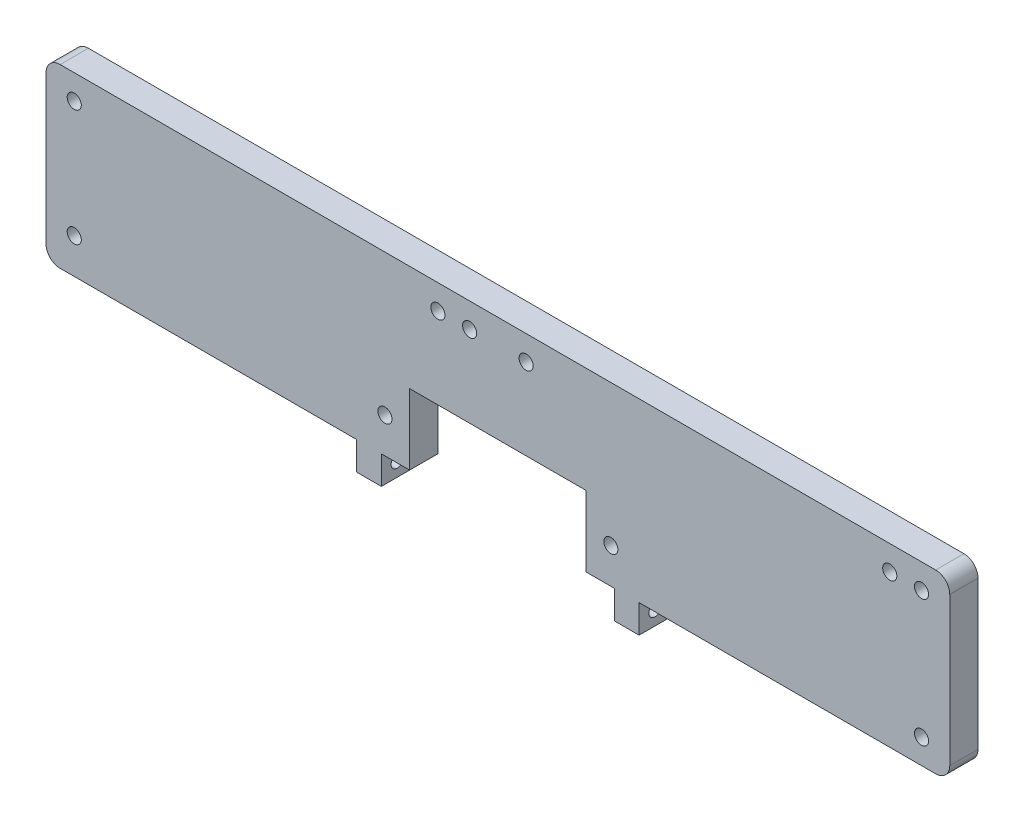
SolidWorks part; units mm, degrees
material "ABS"
ref_plane "Front Plane" through (0, 0, 0) normal (0, 0, 1) x (1, 0, 0)
ref_plane "Top Plane" through (0, 0, 0) normal (0, 1, 0) x (1, 0, 0)
ref_plane "Right Plane" through (0, 0, 0) normal (1, 0, 0) x (0, 0, -1)
sketch "Sketch1" plane through (0, 0, 0) normal (0, 0, 1) x (1, 0, 0)
  line L1 (-127.7162, 72.1061) -> (128.2838, 72.1061)
  line L2 (-127.7162, 72.1061) -> (-127.7162, 22.1061)
  line L3 (-127.7162, 22.1061) -> (128.2838, 22.1061)
  line L4 (128.2838, 72.1061) -> (128.2838, 22.1061)
  circle A1 centre (120.2838, 65.1061) radius 2
  circle A2 centre (111.2838, 65.1061) radius 2
  circle A3 centre (8.2838, 65.1061) radius 2
  circle A4 centre (-7.7162, 65.1061) radius 2
  circle A5 centre (-16.7162, 65.1061) radius 2
  circle A6 centre (-119.7162, 65.1061) radius 2
  dimension "D3" = 4
  dimension "D1" = 256
  dimension "D2" = 50
  dimension "D4" = 7
  dimension "D5" = 9
  dimension "D6" = 8
  dimension "D7" = 103
  dimension "D8" = 16
  dimension "D9" = 9
  dimension "D10" = 103
extrude "Boss-Extrude1" add sketch "Sketch1" along normal blind 8
fillet "Fillet1" radius 4 4 edges at (-127.7162, 22.1061, 4) (128.2838, 22.1061, 4) (128.2838, 72.1061, 4) (-127.7162, 72.1061, 4)
sketch "Sketch2" plane through (0, 0, 8) normal (0, 0, 1) x (1, 0, 0)
  line L0 (-123.7162, 22.1061) -> (124.2838, 22.1061) construction
  line L1 (-24.7162, 34.1061) -> (25.2838, 34.1061)
  line L2 (-24.7162, 34.1061) -> (-24.7162, 22.1061)
  line L3 (-24.7162, 22.1061) -> (25.2838, 22.1061)
  line L4 (25.2838, 34.1061) -> (25.2838, 22.1061)
  line L5 (-127.7162, 68.1061) -> (-127.7162, 26.1061) construction
  line L7 (-32.7162, 22.1061) -> (-39.7162, 22.1061)
  line L8 (-32.7162, 22.1061) -> (-32.7162, 14.1061)
  line L9 (-32.7162, 14.1061) -> (-39.7162, 14.1061)
  line L10 (-39.7162, 22.1061) -> (-39.7162, 14.1061)
  line L11 (33.2838, 22.1061) -> (40.2838, 22.1061)
  line L12 (33.2838, 22.1061) -> (33.2838, 14.1061)
  line L13 (33.2838, 14.1061) -> (40.2838, 14.1061)
  line L14 (40.2838, 22.1061) -> (40.2838, 14.1061)
  line M18 (-123.7162, 22.1061) -> (124.2838, 22.1061)
  dimension "D1" = 50
  dimension "D2" = 12
  dimension "D3" = 103
  dimension "D4" = 7
  dimension "D5" = 8
  dimension "D6" = 8
  dimension "D7" = 8
extrude "Boss-Extrude2" add sketch "Sketch2" against normal blind 8 contours L14 L12 L13 M18 | L8 L7 L10 L9
sketch "Sketch3" plane through (0, 0, 8) normal (0, 0, 1) x (1, 0, 0)
  line L0 (-32.7162, 22.1061) -> (33.2838, 22.1061) construction
  line L1 (-24.7162, 42.1061) -> (25.2838, 42.1061)
  line L2 (-24.7162, 42.1061) -> (-24.7162, 22.1061)
  line L3 (-24.7162, 22.1061) -> (25.2838, 22.1061)
  line L4 (25.2838, 42.1061) -> (25.2838, 22.1061)
  line L5 (-32.7162, 22.1061) -> (-32.7162, 14.1061) construction
  dimension "D1" = 50
  dimension "D2" = 8
  dimension "D3" = 20
extrude "Cut-Extrude1" cut sketch "Sketch3" against normal blind 8
sketch "Sketch4" plane through (0, 0, 8) normal (0, 0, 1) x (1, 0, 0)
  line L0 (-32.7162, 22.1061) -> (-24.7162, 22.1061) construction
  line L1 (-24.7162, 42.1061) -> (-24.7162, 22.1061) construction
  line L2 (25.2838, 22.1061) -> (25.2838, 42.1061) construction
  line L3 (25.2838, 22.1061) -> (33.2838, 22.1061) construction
  line L4 (40.2838, 22.1061) -> (124.2838, 22.1061) construction
  line L5 (128.2838, 26.1061) -> (128.2838, 68.1061) construction
  line L6 (-123.7162, 22.1061) -> (-39.7162, 22.1061) construction
  line L7 (-127.7162, 68.1061) -> (-127.7162, 26.1061) construction
  circle A0 centre (-31.7162, 32.1061) radius 2
  circle A1 centre (32.2838, 32.1061) radius 2
  circle A2 centre (-119.7162, 32.1061) radius 2
  circle A3 centre (120.2838, 29.1061) radius 2
  dimension "D1" = 4
  dimension "D2" = 10
  dimension "D3" = 7
  dimension "D4" = 7
  dimension "D5" = 10
  dimension "D6" = 7
  dimension "D7" = 8
  dimension "D8" = 10
  dimension "D9" = 8
extrude "Cut-Extrude2" cut sketch "Sketch4" against normal blind 8
sketch "Sketch5" plane through (-39.7162, 0, 0) normal (-1, 0, 0) x (0, 0, 1)
  line L0 (0, 22.1061) -> (0, 14.1061) construction
  line L1 (0, 14.1061) -> (8, 14.1061) construction
  circle A0 centre (3.5, 18.1061) radius 1.75
  dimension "D2" = 3.5
  dimension "D1" = 3.5
  dimension "D3" = 4
extrude "Cut-Extrude3" cut sketch "Sketch5" against normal blind 113
